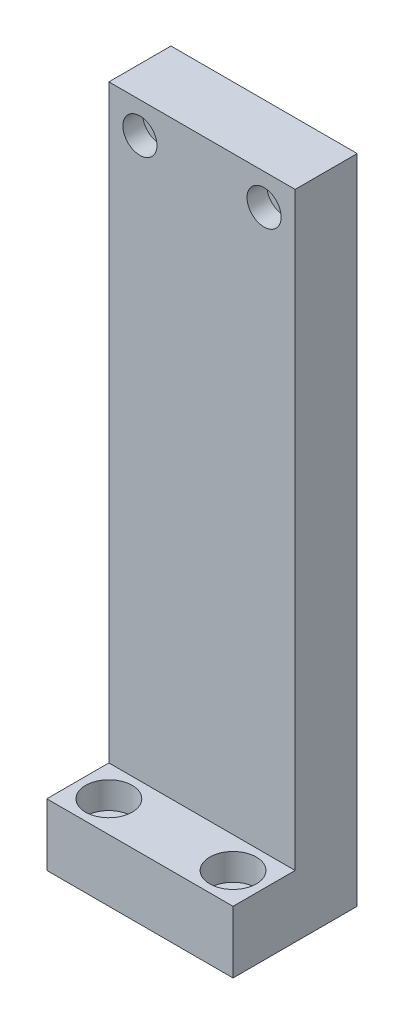
SolidWorks part; units mm, degrees
ref_plane "前视基准面" through (0, 0, 0) normal (0, 0, 1) x (1, 0, 0)
ref_plane "上视基准面" through (0, 0, 0) normal (0, 1, 0) x (1, 0, 0)
ref_plane "右视基准面" through (0, 0, 0) normal (1, 0, 0) x (0, 0, -1)
sketch "草图2" plane through (0, 0, 0) normal (0, 0, 1) x (1, 0, 0)
  line L1 (30, -105) -> (-30, -105)
  line L2 (30, -105) -> (30, 105)
  line L3 (30, 105) -> (-30, 105)
  line L4 (-30, -105) -> (-30, 105)
  line L5 (30, -105) -> (-30, 105) construction
  line L6 (30, 105) -> (-30, -105) construction
  point P0 (0, 0)
  dimension "D1" = 210
  dimension "D2" = 60
extrude "凸台-拉伸1" add sketch "草图2" along normal blind 40
sketch "草图3" plane through (0, 0, 40) normal (0, 0, 1) x (1, 0, 0)
  line L0 (30, 105) -> (-30, 105) construction
  line L1 (-30, 105) -> (30, 105)
  line L2 (-30, 105) -> (-30, -85)
  line L3 (-30, -85) -> (30, -85)
  line L4 (30, 105) -> (30, -85)
  line L5 (30, -105) -> (30, 105) construction
  line L6 (-30, -105) -> (30, -105) construction
  line L7 (-30, 105) -> (-30, -105) construction
  dimension "D1" = 20
extrude "切除-拉伸1" cut sketch "草图3" against normal offset from surface (20 mm away) 20 up to face at (0, 0, 0)
sketch "草图4" plane through (0, 0, 20) normal (0, 0, 1) x (1, 0, 0)
  line L0 (0, 105) -> (0, 75) construction
  line L1 (20, 55) -> (-20, 55)
  line L2 (20, 55) -> (20, 95)
  line L3 (20, 95) -> (-20, 95)
  line L4 (-20, 55) -> (-20, 95)
  line L5 (20, 55) -> (-20, 95) construction
  line L6 (20, 95) -> (-20, 55) construction
  line L7 (-30, 105) -> (30, 105) construction
  point P0 (0, 75)
  dimension "D1" = 10
  dimension "D2" = 40
  dimension "D3" = 40
hole_wizard "M6 六角凹头螺钉的柱形沉头孔2" positions "3D草图1" profile "草图6" counterbore size "M6" standard "Iso" end condition through all
sketch3d "3D草图1"
  point P0 (-20, 95, 20)
  point P3 (20, 95, 20)
sketch "草图6" plane through (-20, 95, 20) normal (1, 0, 0) x (0, -1, 0)
  line L0 (0, 0) -> (0, 20)
  line L1 (0, 20) -> (3.2, 20)
  line L3 (3.2, 20) -> (3.2, 6.4)
  line L4 (3.2, 6.4) -> (5.5, 6.4)
  line L5 (5.5, 6.4) -> (5.5, 0)
  line L7 (5.5, 0) -> (0, 0)
  line L11 (0, -6.35) -> (0, 107.95) construction
  dimension "通孔孔直径" = 6.4
  dimension "通孔孔深度" = 20
  dimension "柱形沉头孔直径" = 11
  dimension "柱形沉头孔深度" = 6.4
sketch "草图8" plane through (0, -85, 0) normal (0, 1, 0) x (1, 0, 0)
  line L0 (-30, -30) -> (30, -30) construction
  line L1 (-30, -20) -> (-30, -40) construction
  line L2 (30, -20) -> (30, -40) construction
  line L3 (0, -30) -> (0, -32.7187) construction
  line L4 (30, -20) -> (-30, -20) construction
  circle A0 centre (-20, -30) radius 4.0202
  circle A1 centre (20, -30) radius 4.0202
  dimension "D1" = 40
  dimension "D2" = 10
hole_wizard "M8 六角凹头螺钉的柱形沉头孔2" positions "3D草图2" profile "草图9" counterbore size "M8" standard "Iso" end condition through all
sketch3d "3D草图2"
  point P0 (-20, -85, 30)
  point P3 (20, -85, 30)
sketch "草图9" plane through (-20, -85, 30) normal (1, 0, 0) x (0, 0, 1)
  line L0 (0, 0) -> (0, 20)
  line L1 (0, 20) -> (4.2, 20)
  line L3 (4.2, 20) -> (4.2, 8.6)
  line L4 (4.2, 8.6) -> (7.5, 8.6)
  line L5 (7.5, 8.6) -> (7.5, 0)
  line L7 (7.5, 0) -> (0, 0)
  line L11 (0, -6.35) -> (0, 107.95) construction
  dimension "通孔孔直径" = 8.4
  dimension "通孔孔深度" = 20
  dimension "柱形沉头孔直径" = 15
  dimension "柱形沉头孔深度" = 8.6
